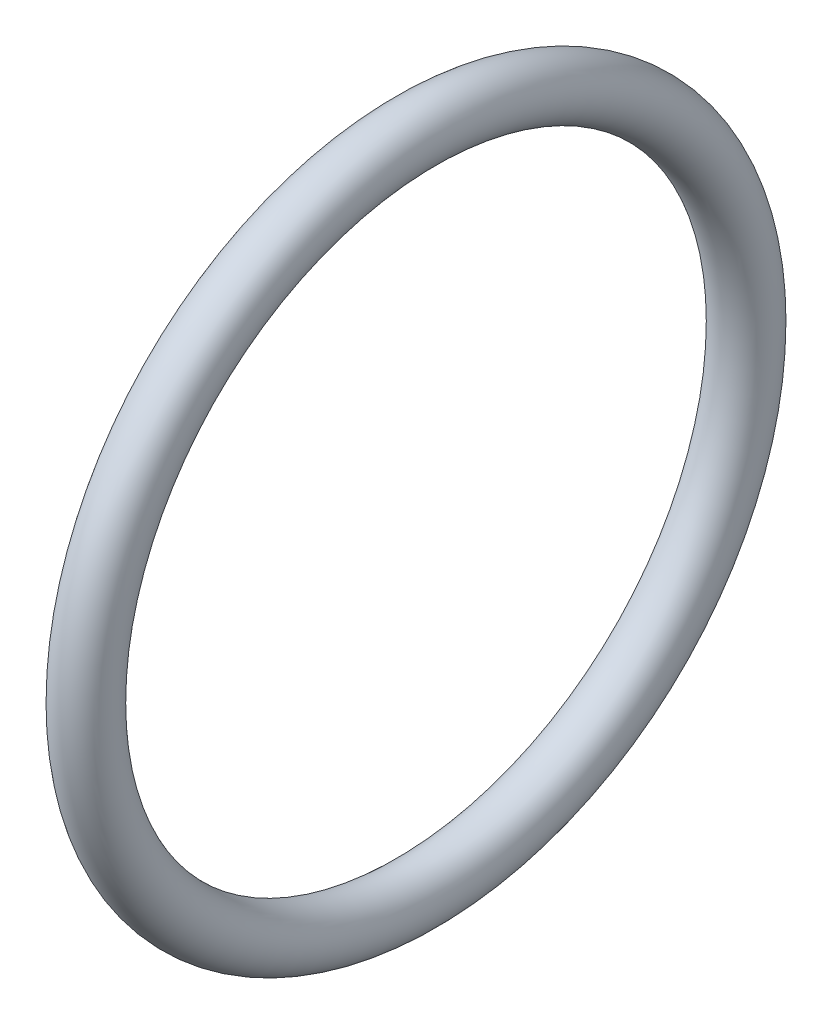
SolidWorks part; units mm, degrees
ref_plane "Front Plane" through (0, 0, 0) normal (0, 0, 1) x (1, 0, 0)
ref_plane "Top Plane" through (0, 0, 0) normal (0, 1, 0) x (1, 0, 0)
ref_plane "Right Plane" through (0, 0, 0) normal (1, 0, 0) x (0, 0, -1)
sketch "Sketch2" plane through (0, 0, 0) normal (0, 0, 1) x (1, 0, 0)
  line L0 (0, 0) -> (58.591, 0) construction
  line L2 (0, 0) -> (18.4, 0)
  line L3 (0, 0) -> (0, 2.5)
  line L4 (0, 2.5) -> (18.4, 2.5)
  line L5 (18.4, 0) -> (18.4, 2.5)
  line L6 (6.0094, 2.5) -> (6.0094, 6)
  line L11 (6.0094, 6) -> (9.9794, 6)
  line L16 (12.9794, 6) -> (12.9794, 3)
  line L17 (12.9794, 3) -> (13.6398, 3)
  line L18 (13.6398, 3) -> (13.6398, 2.5)
  line L19 (13.6398, 2.5) -> (6.0094, 2.5)
  line L22 (13.6398, 2.5) -> (16.1198, 2.5)
  line L23 (13.6398, 2.5) -> (13.6398, 4)
  line L24 (13.6398, 4) -> (16.1198, 4)
  line L25 (16.1198, 2.5) -> (16.1198, 4)
  line L27 (6.0094, 6) -> (9.9794, 6)
  line L28 (6.0094, 6) -> (6.0094, 9)
  line L29 (6.0094, 9) -> (9.9794, 9)
  line L30 (9.9794, 6) -> (9.9794, 9)
  line L31 (6.0094, 9) -> (6.0094, 8.25)
  line L32 (6.0094, 8.25) -> (5.0094, 8.25)
  line L33 (8.6609, 22.001) -> (8.6609, 12.476) construction
  line L34 (5.0094, 12.476) -> (12.3124, 12.476)
  line L35 (9.9794, 9) -> (12.3124, 9)
  line L36 (5.0094, 7.9375) -> (1.7709, 7.9375)
  line L37 (5.0094, 8.25) -> (5.0094, 12.476)
  line L38 (5.0094, 7.9375) -> (5.0094, 13.9365)
  line L39 (5.0094, 13.9365) -> (1.7709, 13.9365)
  line L40 (1.7709, 7.9375) -> (1.7709, 13.9365)
  line L41 (5.0094, 22.001) -> (12.3124, 22.001)
  line L42 (5.0094, 22.001) -> (5.0094, 30.1625)
  line L43 (5.0094, 30.1625) -> (12.3124, 30.1625)
  line L44 (12.3124, 22.001) -> (12.3124, 30.1625)
  line L49 (16.6398, 22.001) -> (16.6398, 7.5)
  line L51 (23.0198, 7.5) -> (23.0198, 6.5)
  line L54 (16.1198, 4) -> (13.6398, 4)
  line L56 (18.0398, 7.5) -> (23.0198, 7.5)
  line L57 (13.3124, 22.001) -> (16.6398, 22.001)
  line L58 (16.1198, 3.5) -> (20.0198, 3.5)
  line L59 (29.9098, 14) -> (26.9098, 11)
  line L60 (4.0094, 31.75) -> (18.0398, 31.75)
  line L61 (18.0398, 7.5) -> (23.0198, 7.5)
  line L62 (18.0398, 7.5) -> (18.0398, 12)
  line L63 (18.0398, 12) -> (23.0198, 12)
  line L64 (23.0198, 7.5) -> (23.0198, 12)
  line L65 (18.0398, 31.75) -> (18.0398, 12)
  line L66 (23.0198, 11) -> (26.9098, 11)
  line L67 (34.8098, 23) -> (31.3098, 19.5)
  line L68 (35.8098, 31) -> (38.7998, 33.99)
  line L69 (29.9098, 14) -> (29.9098, 15)
  line L70 (29.9098, 15) -> (22.9398, 15)
  line L71 (22.9398, 15) -> (21.0398, 15)
  line L72 (18.0398, 7.5) -> (16.6398, 7.5)
  line L73 (21.0398, 15) -> (21.0398, 43)
  line L74 (19.6115, 40) -> (9.6516, 40)
  line L75 (9.6516, 40) -> (4.0094, 40)
  line L76 (21.0398, 43) -> (19.6115, 43)
  line L77 (22.9398, 15) -> (29.9098, 15)
  line L78 (22.9398, 15) -> (22.9398, 21)
  line L79 (22.9398, 21) -> (29.9098, 21)
  line L80 (29.9098, 15) -> (29.9098, 21)
  line L81 (9.6516, 40) -> (19.6115, 40)
  line L82 (9.6516, 40) -> (9.6516, 50)
  line L83 (9.6516, 50) -> (19.6115, 50)
  line L84 (19.6115, 40) -> (19.6115, 50)
  line L85 (4.0094, 40) -> (4.0094, 31.75)
  line L86 (12.9794, 3) -> (12.9794, 2.5)
  line L87 (31.3098, 19.5) -> (29.9098, 19.5)
  line L88 (21.4694, 63.5) -> (21.4694, 51.308)
  line L89 (21.4694, 63.5) -> (25.9398, 63.5)
  line L90 (25.9398, 63.5) -> (25.9398, 25)
  line L91 (27.8398, 25) -> (25.9398, 25)
  line L92 (9.6516, 48) -> (8.2233, 48)
  line L93 (8.2233, 48) -> (8.2233, 53.476)
  line L94 (8.2233, 53.476) -> (19.6115, 53.476)
  line L95 (19.6115, 53.476) -> (19.6115, 50)
  line L96 (13.9174, 63.001) -> (13.9174, 53.476) construction
  line L97 (8.2233, 63.001) -> (19.6115, 63.001)
  line L98 (8.2233, 63.001) -> (8.2233, 68.2625)
  line L99 (8.2233, 68.2625) -> (19.6115, 68.2625)
  line L100 (19.6115, 63.001) -> (19.6115, 68.2625)
  line L101 (12.9794, 6) -> (11.9794, 6)
  line L102 (8.2233, 44.825) -> (4.9848, 44.825)
  line L103 (8.2233, 44.825) -> (8.2233, 54.9365)
  line L104 (8.2233, 54.9365) -> (4.9848, 54.9365)
  line L106 (9.9794, 6) -> (10.8794, 6)
  line L107 (27.8398, 25) -> (34.8098, 25)
  line L108 (34.8098, 25) -> (34.8098, 23)
  line L109 (0, 0) -> (-2, 0)
  line L110 (0, 0) -> (0, 11)
  line L111 (27.8398, 25) -> (34.8098, 25)
  line L112 (27.8398, 25) -> (27.8398, 32.5)
  line L113 (27.8398, 32.5) -> (34.8098, 32.5)
  line L114 (34.8098, 25) -> (34.8098, 32.5)
  line L115 (35.8098, 31) -> (34.8098, 31)
  line L116 (27.8398, 32.5) -> (27.8398, 64.5)
  line L117 (20.5849, 74.025) -> (6.2499, 74.025)
  line L118 (6.2499, 74.025) -> (6.2499, 76.2)
  line L119 (38.7998, 47.29) -> (30.8398, 55.25)
  line L120 (0, 11) -> (-2, 11)
  line L121 (38.7998, 43.815) -> (30.8623, 43.815)
  line L123 (-4.8152, 69.85) -> (1.5348, 76.2)
  line L124 (38.7998, 47.29) -> (38.7998, 33.99)
  line L125 (-2, 0) -> (-2, 11)
  line L126 (38.7998, 37.465) -> (30.8623, 37.465)
  line L127 (30.8623, 43.815) -> (30.8623, 37.465)
  line L128 (6.0094, 2.5) -> (6.0094, 0)
  line L129 (-0.0152, 63.5) -> (-0.0152, 30)
  line L132 (4.9848, 63.5) -> (-0.0152, 63.5)
  line L136 (-1.8152, 30) -> (-11.7752, 30)
  line L138 (-13.7752, 25.4) -> (-2, 25.4)
  line L139 (-2, 25.4) -> (-2, 11.5)
  line L140 (27.8398, 64.5) -> (20.5849, 64.5)
  line L141 (-1.8152, 30) -> (-11.7752, 30)
  line L142 (-1.8152, 30) -> (-1.8152, 39)
  line L143 (-1.8152, 39) -> (-11.7752, 39)
  line L144 (-11.7752, 30) -> (-11.7752, 39)
  line L145 (20.5849, 64.5) -> (20.5849, 74.025)
  line L146 (-12.7752, 37) -> (-12.7752, 47.29)
  line L147 (-12.7752, 37) -> (-11.7752, 37)
  line L148 (30.8398, 55.25) -> (30.8398, 76.2)
  line L149 (11.9794, 6) -> (11.9794, 5.45)
  line L154 (-2, 11.5) -> (0.5, 11.5)
  line L155 (4.9848, 60.6197) -> (24.0348, 60.6197)
  line L160 (4.9848, 60.6197) -> (4.9848, 55.8572)
  line L161 (4.9848, 55.8572) -> (24.0348, 55.8572)
  line L166 (24.0348, 60.6197) -> (24.0348, 55.8572)
  line L167 (4.9848, 60.6197) -> (24.0348, 55.8572) construction
  line L172 (4.9848, 55.8572) -> (24.0348, 60.6197) construction
  line L173 (24.0348, 62.2072) -> (25.9398, 62.2072)
  line L174 (11.9794, 5.45) -> (10.8794, 5.45)
  line L175 (10.8794, 6) -> (10.8794, 5.45)
  line L176 (24.0348, 62.2072) -> (24.0348, 54.2697)
  line L177 (24.0348, 54.2697) -> (25.9398, 54.2697)
  line L178 (25.9398, 62.2072) -> (25.9398, 54.2697)
  line L179 (24.0348, 62.2072) -> (25.9398, 54.2697) construction
  line L180 (24.0348, 54.2697) -> (25.9398, 62.2072) construction
  line L181 (3, 19.6197) -> (15.7, 19.6197)
  line L182 (3, 19.6197) -> (3, 14.8572)
  line L183 (3, 14.8572) -> (15.7, 14.8572)
  line L184 (15.7, 19.6197) -> (15.7, 14.8572)
  line L185 (3, 19.6197) -> (15.7, 14.8572) construction
  line L186 (3, 14.8572) -> (15.7, 19.6197) construction
  line L187 (15.7, 21.2072) -> (16.6398, 21.2072)
  line L188 (15.7, 21.2072) -> (15.7, 13.2697)
  line L189 (15.7, 13.2697) -> (16.6398, 13.2697)
  line L190 (16.6398, 21.2072) -> (16.6398, 13.2697)
  line L191 (15.7, 21.2072) -> (16.6398, 13.2697) construction
  line L192 (15.7, 13.2697) -> (16.6398, 21.2072) construction
  line L193 (0.5, 11.5) -> (0.5, 6.9375)
  line L194 (0.5, 6.9375) -> (1.7709, 6.9375)
  line L195 (23.0198, 6.5) -> (20.0198, 3.5)
  line L196 (4.9848, 63.5) -> (4.9848, 54.9365)
  line L197 (3, 43.825) -> (4.9848, 43.825)
  line L198 (1.7709, 6.9375) -> (1.7709, 7.9375)
  line L199 (6.0094, 0) -> (12.9794, 0)
  line L200 (12.9794, 0) -> (12.9794, 2.5)
  line L201 (18.0398, 31.75) -> (18.0398, 35.875)
  line L202 (18.0398, 35.875) -> (21.0398, 35.875)
  line L203 (30.8398, 76.2) -> (6.2499, 76.2)
  line L204 (2.8049, 69.85) -> (7.2499, 69.85) construction
  line L205 (7.2499, 67.4688) -> (26.2999, 67.4688)
  line L206 (7.2499, 74.025) -> (7.2499, 64.5)
  line L207 (7.2499, 64.5) -> (-1.8152, 64.5)
  line L208 (-1.8152, 64.5) -> (-1.8152, 39)
  line L209 (-12.7752, 47.29) -> (-4.8152, 55.25)
  line L210 (-4.8152, 55.25) -> (-4.8152, 69.85)
  line L211 (7.2499, 67.4688) -> (7.2499, 72.2312)
  line L212 (7.2499, 72.2312) -> (26.2999, 72.2313)
  line L213 (26.2999, 67.4688) -> (26.2999, 72.2313)
  line L214 (26.2999, 73.8187) -> (30.8398, 73.8187)
  line L215 (26.2999, 73.8187) -> (26.2999, 65.8813)
  line L216 (26.2999, 65.8813) -> (30.8398, 65.8813)
  line L217 (30.8398, 73.8187) -> (30.8398, 65.8813)
  line L218 (2.8049, 72.2313) -> (25.0299, 72.2313)
  line L219 (2.8049, 72.2313) -> (2.8049, 67.4687)
  line L220 (2.8049, 67.4687) -> (25.0299, 67.4687)
  line L221 (25.0299, 72.2313) -> (25.0299, 67.4687)
  line L222 (25.0299, 69.85) -> (20.5849, 69.85) construction
  line L223 (21.4694, 51.308) -> (22.9398, 51.308)
  line L224 (22.9398, 51.308) -> (22.9398, 21)
  line L225 (13.6398, 4) -> (13.6398, 12.2697)
  line L226 (13.6398, 12.2697) -> (13.3124, 12.2697)
  line L227 (13.3124, 12.2697) -> (13.3124, 22.001)
  line L228 (12.3124, 9) -> (12.3124, 12.476)
  line L229 (-1.8152, 30) -> (-0.0152, 30)
  line L230 (8.2233, 65.6317) -> (2.8049, 65.6317) construction
  line L231 (19.6115, 65.6317) -> (25.0299, 65.6317) construction
  line L232 (1.5348, 76.2) -> (6.2499, 76.2)
  line L233 (-11.7752, 30) -> (-13.7752, 30)
  line L234 (-13.7752, 30) -> (-13.7752, 25.4)
  line L235 (3, 13.9365) -> (3, 43.825)
  line L236 (4.9848, 54.9365) -> (4.9848, 44.825)
  line L237 (4.9848, 43.825) -> (4.9848, 44.825)
  circle A0 centre (26.8898, 25.95) radius 0.95
  circle A1 centre (21.9898, 15.95) radius 0.95
  circle A2 centre (17.3398, 8.2) radius 0.7
  circle A3 centre (10.4294, 6.45) radius 0.45
  circle A4 centre (-0.9152, 30.9) radius 0.9
  point P7 (24.9873, 58.2385)
  point P131 (16.1699, 17.2385)
  point P135 (14.5098, 58.2385)
  point P146 (9.35, 17.2385)
sketch "Sketch3" plane through (0, 0, 0) normal (0, 0, 1) x (1, 0, 0)
  circle A0 centre (17.3398, 8.2) radius 0.7 construction
  circle A1 centre (17.3398, 8.2) radius 0.7
revolve "Revolve1" add sketch "Sketch3" angle 360 about L0
